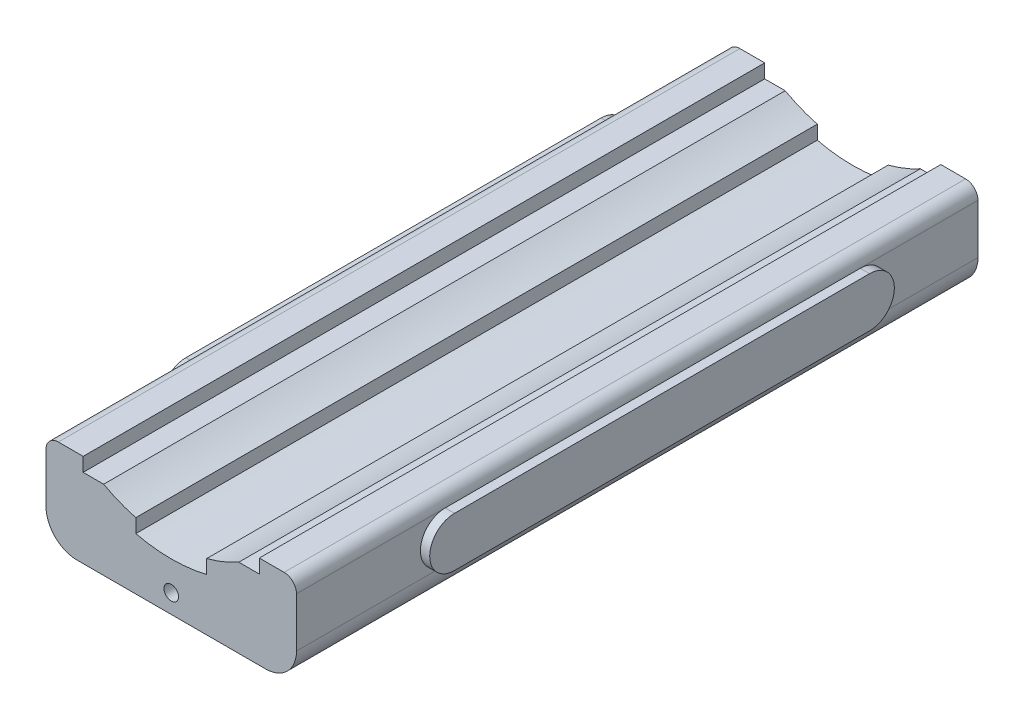
SolidWorks part; units mm, degrees
ref_plane "Front Plane" through (0, 0, 0) normal (0, 0, 1) x (1, 0, 0)
ref_plane "Top Plane" through (0, 0, 0) normal (0, 1, 0) x (1, 0, 0)
ref_plane "Right Plane" through (0, 0, 0) normal (1, 0, 0) x (0, 0, -1)
sketch "Sketch1" plane through (0, 0, 0) normal (0, 0, 1) x (1, 0, 0)
  line L0 (6.6209, -4.4806) -> (0, -4.4806)
  line L1 (0, -4.4806) -> (0, 0)
  line L2 (0, 0) -> (-12, 0)
  line L3 (56.8632, 0) -> (56.8632, -4.4806)
  line L4 (56.8632, -4.4806) -> (50.2423, -4.4806)
  line L5 (16.9859, -8.6396) -> (16.9859, -13.1203)
  line L6 (39.8773, -8.6396) -> (39.8773, -13.1203)
  line L7 (56.8632, 0) -> (68.8632, 0)
  line L8 (-12, 0) -> (-12, -30)
  line L9 (68.8632, 0) -> (68.8632, -30)
  line L10 (-12, -30) -> (68.8632, -30)
  arc A0 (16.9859, -13.1203) -> (39.8773, -13.1203) centre (28.4316, 34.8804) ccw
  arc A1 (6.6209, -4.4806) -> (16.9859, -8.6396) centre (28.4316, 34.8804) ccw
  arc A2 (39.8773, -8.6396) -> (50.2423, -4.4806) centre (28.4316, 34.8804) ccw
extrude "Boss-Extrude1" add sketch "Sketch1" along normal blind 220 contours A2 L6 A0 L5 A1 L0 L1 L2 L8 L10 L9 L7 L3 L4
fillet "Fillet1" radius 4 2 edges at (-12, 0, 110) (68.8632, 0, 110)
fillet "Fillet2" radius 10 2 edges at (68.8632, -30, 110) (-12, -30, 110)
sketch "Sketch6" plane through (68.8632, 0, 0) normal (1, 0, 0) x (0, 0, -1)
  line L2 (0, -4) -> (-220, -4) construction
  line L3 (-180, -4) -> (-30, -4)
  line L4 (-180, -4) -> (-180, -20)
  line L5 (-180, -20) -> (-30, -20)
  line L6 (-30, -4) -> (-30, -20)
  line L7 (-220, -20) -> (0, -20) construction
extrude "Boss-Extrude2" add sketch "Sketch6" along normal blind 3
sketch "Sketch7" plane through (-12, 0, 0) normal (-1, 0, 0) x (0, 0, 1)
  line L2 (220, -4) -> (0, -4) construction
  line L3 (179.8243, -4) -> (29.8243, -4)
  line L4 (179.8243, -4) -> (179.8243, -20)
  line L5 (179.8243, -20) -> (29.8243, -20)
  line L6 (29.8243, -4) -> (29.8243, -20)
  line L7 (0, -20) -> (220, -20) construction
extrude "Boss-Extrude3" add sketch "Sketch7" along normal blind 3
sketch "Sketch8" plane through (-15, 0, 0) normal (-1, 0, 0) x (0, 0, 1)
  line L0 (37.8243, -4) -> (29.8243, -4)
  line L2 (179.8243, -4) -> (29.8243, -4) construction
  line L3 (29.8243, -20) -> (179.8243, -20) construction
  line L4 (29.8243, -4) -> (29.8243, -20)
  line L5 (29.8243, -20) -> (37.8243, -20)
  line L7 (179.8243, -20) -> (171.8243, -20)
  line L8 (179.8243, -4) -> (179.8243, -20)
  line L9 (171.8243, -4) -> (179.8243, -4)
  arc A0 (37.8243, -4) -> (37.8243, -20) centre (37.8243, -12) ccw
  arc A1 (171.8243, -4) -> (171.8243, -20) centre (171.8243, -12) cw
  line M4 (179.8243, -20) -> (179.8243, -4)
  line M5 (179.8243, -4) -> (29.8243, -4)
  line M6 (29.8243, -4) -> (29.8243, -20)
  line M7 (29.8243, -20) -> (179.8243, -20)
extrude "Cut-Extrude1" cut sketch "Sketch8" against normal blind 3 contours A0 L4 M7 | A0 M5 M6 | A1 M4 M7 | A1 L8 M5
sketch "Sketch9" plane through (71.8632, 0, 0) normal (1, 0, 0) x (0, 0, -1)
  line L2 (-30, -4) -> (-180, -4) construction
  line L3 (-180, -20) -> (-30, -20) construction
  line L4 (-172, -4) -> (-180, -4)
  line L5 (-180, -4) -> (-180, -20)
  line L6 (-180, -20) -> (-172, -20)
  line L7 (-30, -20) -> (-38, -20)
  line L8 (-30, -4) -> (-30, -20)
  line L9 (-38, -4) -> (-30, -4)
  arc A0 (-172, -4) -> (-172, -20) centre (-172, -12) ccw
  arc A1 (-38, -4) -> (-38, -20) centre (-38, -12) cw
  line M3 (-180, -4) -> (-180, -20)
  line M4 (-180, -20) -> (-30, -20)
  line M5 (-30, -20) -> (-30, -4)
  line M6 (-30, -4) -> (-180, -4)
extrude "Cut-Extrude2" cut sketch "Sketch9" against normal blind 3 contours A0 M6 M3 | A0 L5 M4 | A1 L8 M6 | A1 M5 M4
sketch "Sketch10" plane through (0, 0, 220) normal (0, 0, 1) x (1, 0, 0)
  circle A0 centre (28.4316, -23.8942) radius 2.3419
extrude "Cut-Extrude3" cut sketch "Sketch10" against normal blind 5
scale "Scale1" scale about centroid uniform scaling yes scale factor 15.6
scale "Scale2" scale about centroid uniform scaling yes scale factor 0.5
